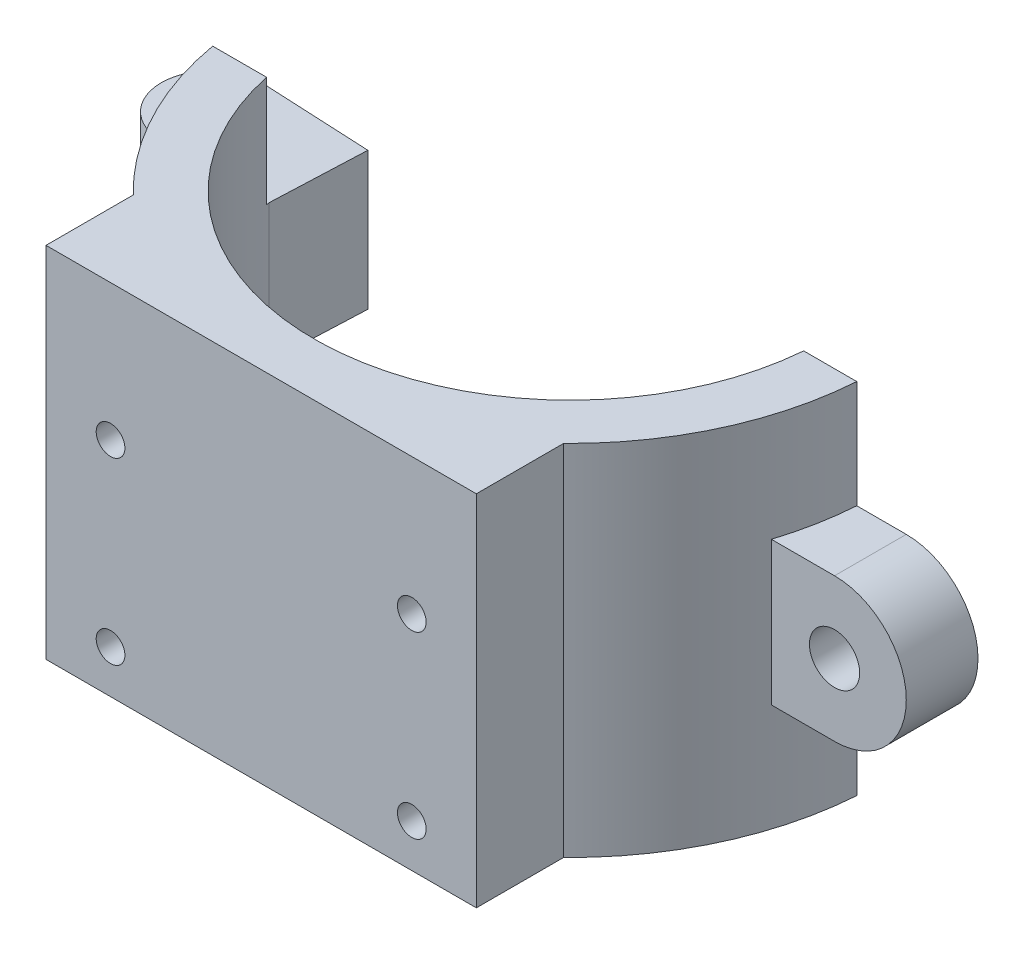
SolidWorks part; units mm, degrees
ref_plane "Plan de face" through (0, 0, 0) normal (0, 0, 1) x (1, 0, 0)
ref_plane "Plan de dessus" through (0, 0, 0) normal (0, 1, 0) x (1, 0, 0)
ref_plane "Plan de droite" through (0, 0, 0) normal (1, 0, 0) x (0, 0, -1)
sketch "Esquisse1" plane through (0, 0, 0) normal (0, 1, 0) x (1, 0, 0)
  line L0 (-25, -5) -> (-17.5, -5) construction
  line L1 (17.7834, -3) -> (21.484, -3)
  line L2 (21.4476, 0) -> (17.4356, 0) construction
  line L3 (-21.25, -5) -> (-17.5, -5)
  arc A0 (-17.5, -5) -> (17.7834, -3) centre (0, -1.5) ccw
  arc A1 (17.4356, 0) -> (-17.5, -1.5) centre (0, -1.5) ccw construction
  arc A2 (-21.25, -5) -> (21.484, -3) centre (0, -1.5) ccw
  arc A3 (21.4476, 0) -> (-21.2132, 2) centre (0, -1.5) ccw construction
  dimension "D1" = 3
extrude "Boss.-Extru.1" add sketch "Esquisse1" against normal up to surface (25 mm away)
sketch "Esquisse2" plane through (0, -17.5, 0) normal (0, 1, 0) x (1, 0, 0)
  line L0 (-17.5, -5) -> (-25, -5) construction
  line L1 (-17.5, -1.5) -> (-17.5, -5) construction
  line L2 (-17.5, -5) -> (-25, -5)
  line L3 (-17.2195, 1.6208) -> (-25, 2)
  line L4 (-17.5, -5) -> (-17.2195, 1.6208)
  arc A0 (-25, -5) -> (-25, 2) centre (-25, -1.5) cw
  circle A1 centre (-25, -1.5) radius 1.5
  circle A2 centre (-25, -1.5) radius 1.5 construction
  arc A3 (-17.1464, 2) -> (-17.5, -1.5) centre (0, -1.5) ccw construction
  point P15 (-17.1464, 2)
  point P19 (-17.2195, 1.6208)
extrude "Boss.-Extru.2" add sketch "Esquisse2" along normal blind 9.8
sketch "Esquisse3" plane through (0, -17.5, 0) normal (0, -1, 0) x (1, 0, 0)
  line L0 (-17.5, 5) -> (-21.25, 5) construction
  line L1 (-10.6949, 5) -> (-41.8717, 5)
  line L2 (-10.6949, 5) -> (-10.6949, -12.8495)
  line L3 (-10.6949, -12.8495) -> (-41.8717, -12.8495)
  line L4 (-41.8717, 5) -> (-41.8717, -12.8495)
extrude "Enlèv. mat.-Extru.2" cut sketch "Esquisse3" against normal blind 0.2
sketch "Esquisse4" plane through (0, 0, 3) normal (0, 0, -1) x (-1, 0, 0)
  line L0 (-17.7834, -17.5) -> (-24.9356, -17.5)
  line L1 (-17.7834, -25) -> (-17.7834, 0) construction
  line L2 (-17.7834, -17.5) -> (-17.7834, -7.5)
  line L3 (-17.7834, -7.5) -> (-24.9356, -7.5)
  line L4 (-24.9356, -7.5) -> (-21.4476, -7.5) construction
  line L5 (-21.4476, -17.5) -> (-24.9356, -17.5) construction
  arc A0 (-24.9356, -17.5) -> (-24.9356, -7.5) centre (-24.9356, -12.5) cw
  arc A1 (-24.9356, -7.5) -> (-24.9356, -17.5) centre (-24.9356, -12.5) ccw construction
  circle A2 centre (-24.9356, -12.5) radius 1.75
  dimension "D1" = 3.5
extrude "Boss.-Extru.3" add sketch "Esquisse4" against normal blind 5
sketch "Esquisse5" plane through (0, 0, 0) normal (0, 1, 0) x (1, 0, 0)
  line L0 (-17.5, -5) -> (-21.25, -5) construction
  line L1 (-23.5438, -5.2) -> (-8.6054, -5.2)
  line L2 (-23.5438, -5.2) -> (-23.5438, -1.5058)
  line L3 (-23.5438, -1.5058) -> (-8.6054, -1.5058)
  line L4 (-8.6054, -5.2) -> (-8.6054, -1.5058)
  dimension "D1" = 0.2
extrude "Enlèv. mat.-Extru.3" cut sketch "Esquisse5" against normal up to surface (7.7 mm away) up to face at (-21.8939, -7.7, 2.2758)
sketch "Esquisse6" plane through (0, -25, 0) normal (0, -1, 0) x (1, 0, 0)
  line L0 (-21.25, 5) -> (-17.5, 5) construction
  line L1 (-15.1624, 5.2) -> (-23.1349, 5.2)
  line L2 (-15.1624, 5.2) -> (-15.1624, 1.7826)
  line L3 (-15.1624, 1.7826) -> (-23.1349, 1.7826)
  line L4 (-23.1349, 5.2) -> (-23.1349, 1.7826)
  dimension "D1" = 0.2
extrude "Enlèv. mat.-Extru.4" cut sketch "Esquisse6" against normal up to surface (7.7 mm away) up to face at (-25, -17.3, 3)
sketch "Esquisse7" plane through (0, 0, 0) normal (0, 1, 0) x (1, 0, 0)
  line L0 (0, -1.5) -> (0, -30.5067) construction
  line L2 (15, -11.1695) -> (15, -23.0363)
  line L3 (15, -23.0363) -> (-15, -23.0363)
  line L4 (-15, -11.1695) -> (-15, -23.0363)
  arc A0 (-21.2161, -5.2) -> (21.484, -3) centre (0, -1.5) ccw construction
  arc A1 (-17.4588, -5.2) -> (17.7834, -3) centre (0, -1.5) ccw construction
  arc A2 (15, -11.1695) -> (-15, -11.1695) centre (0, -1.5) cw
  dimension "D1" = 30
extrude "Boss.-Extru.4" add sketch "Esquisse7" against normal up to surface (25 mm away) up to face at (0.6291, -25, 12.6299)
sketch "Esquisse8" plane through (0, 0, 23.0363) normal (0, 0, 1) x (1, 0, 0)
  line L0 (0, -8.113) -> (0, -21.2072) construction
  line L1 (7.5132, -15.75) -> (-8.1836, -15.75) construction
  line L2 (15, -25) -> (15, 0) construction
  line L3 (-15, -25) -> (-15, 0) construction
  line L4 (15, -25) -> (-15, -25) construction
  circle A0 centre (10.5, -22) radius 1
  circle A1 centre (-10.5, -22) radius 1
  circle A2 centre (10.5, -9.5) radius 1
  circle A3 centre (-10.5, -9.5) radius 1
  point P17 (-10.5, -7.6047)
  dimension "D1" = 12.5
  dimension "D3" = 2
  dimension "D2" = 21
  dimension "D4" = 3
extrude "Enlèv. mat.-Extru.5" cut sketch "Esquisse8" against normal blind 5
